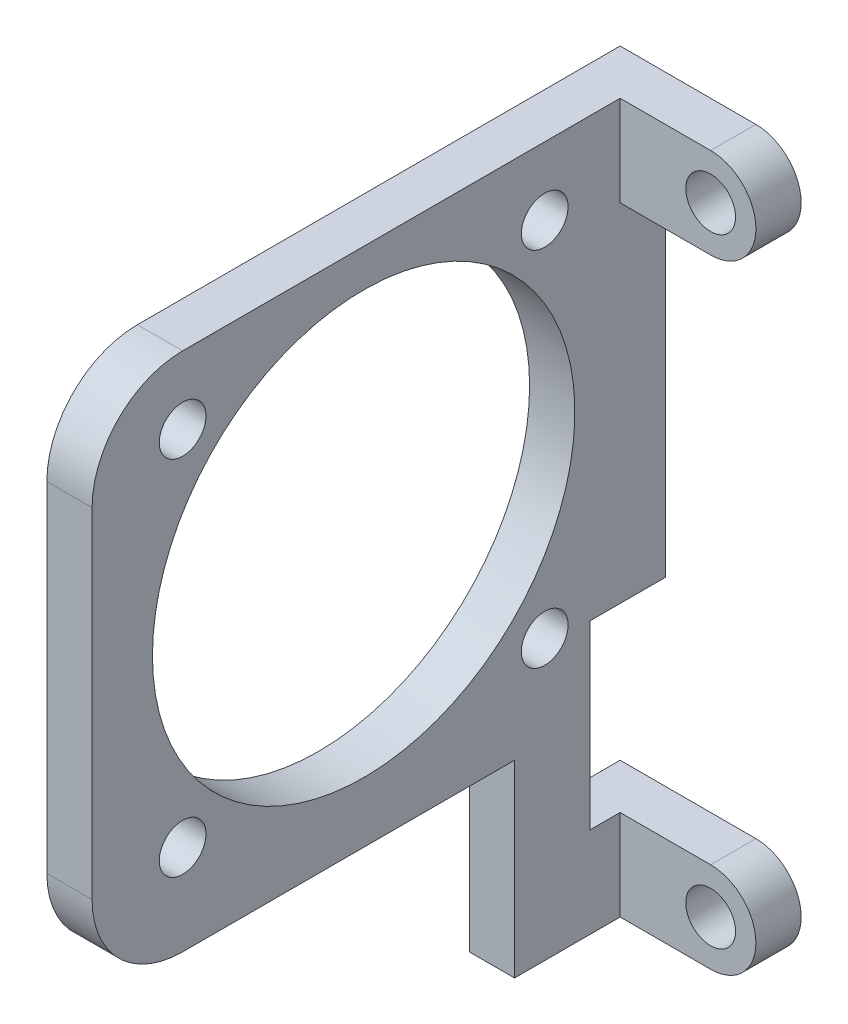
SolidWorks part; units mm, degrees
ref_plane "Plano frontal" through (0, 0, 0) normal (0, 0, 1) x (1, 0, 0)
ref_plane "Plano superior" through (0, 0, 0) normal (0, 1, 0) x (1, 0, 0)
ref_plane "Plano direito" through (0, 0, 0) normal (1, 0, 0) x (0, 0, -1)
sketch "Esboço1" plane through (0, 0, 0) normal (0, 0, 1) x (1, 0, 0)
  line L0 (0, 23.5) -> (-9, 23.5)
  line L1 (-9, 23.5) -> (-9, -23.5)
  line L2 (-9, -23.5) -> (0, -23.5)
  line L3 (0, -17.5) -> (-6, -17.5)
  line L4 (-6, -17.5) -> (-6, 17.5)
  line L5 (-6, 17.5) -> (0, 17.5)
  circle A0 centre (0, 20.5) radius 1.65
  circle A1 centre (0, -20.5) radius 1.65
  arc A2 (0, -23.5) -> (0, -17.5) centre (0, -20.5) ccw
  arc A3 (0, 17.5) -> (0, 23.5) centre (0, 20.5) ccw
  point P13 (-6, 14.9908)
  point P15 (0, 0)
  point P17 (-6, 17.4419)
  point P18 (-6, 0)
  dimension "D2" = 3.3
  dimension "D3" = 6
  dimension "D1" = 41
  dimension "D4" = 3
  dimension "D5" = 3
extrude "Ressalto-extrusão1" add sketch "Esboço1" along normal blind 40
sketch "Esboço2" plane through (0, -23.5, 0) normal (0, -1, 0) x (1, 0, 0)
  line L0 (-6, 40) -> (-6, 3)
  line L1 (-9, 40) -> (0, 40) construction
  line L2 (-6, 3) -> (3, 3)
  line L3 (3, 0) -> (3, 40) construction
  line L4 (3, 3) -> (3, 40)
  line L5 (3, 40) -> (-6, 40)
  line L6 (-9, 0) -> (0, 0) construction
  point P11 (0, 0)
  dimension "D1" = 3
extrude "Corte-extrusão1" cut sketch "Esboço2" against normal through all
sketch "Esboço3" plane through (-9, 0, 0) normal (-1, 0, 0) x (0, 0, 1)
  line L0 (20, 9.4942) -> (20, 7) construction
  line L1 (20, 7) -> (28.7758, 7) construction
  line L2 (0, 23.5) -> (0, -23.5) construction
  line L3 (5, -5.5) -> (0, -5.5)
  line L4 (5, -5.5) -> (5, -17.5)
  line L5 (5, -17.5) -> (0, -17.5)
  line L6 (0, -5.5) -> (0, -17.5)
  line L7 (5, -5.5) -> (0, -17.5) construction
  line L8 (5, -17.5) -> (0, -5.5) construction
  line L9 (40, 23.5) -> (0, 23.5) construction
  line L10 (10, -23.5) -> (10, -11)
  line L11 (40, -23.5) -> (0, -23.5) construction
  line L12 (10, -11) -> (38, -11)
  line L13 (40, 23.5) -> (40, -23.5) construction
  line L14 (40, -8) -> (40, -23.5)
  line L15 (40, -23.5) -> (10, -23.5)
  line L16 (38, 23.5) -> (38, -11)
  line L17 (38, 23.5) -> (40, 23.5)
  line L18 (40, 23.5) -> (40, -8)
  circle A0 centre (20, 7) radius 14
  circle A1 centre (32, 19) radius 1.55
  circle A2 centre (32, -5) radius 1.55
  circle A3 centre (8, -5) radius 1.55
  circle A4 centre (8, 19) radius 1.55
  point P13 (2.5, -11.5)
  point P33 (28.7758, 8)
  dimension "D1" = 3.1
  dimension "D4" = 28
  dimension "D2" = 24
  dimension "D3" = 24
  dimension "D5" = 12
  dimension "D6" = 5
  dimension "D7" = 16.5
  dimension "D8" = 15
  dimension "D9" = 18
  dimension "D10" = 18
  dimension "D11" = 5
extrude "Corte-extrusão2" cut sketch "Esboço3" against normal up to surface (3 mm away) and the other way through all up to face at (-6, 0, 11.5)
fillet "Filete1" radius 6 2 edges at (-7.5, 23.5, 38) (-7.5, -11, 38)
